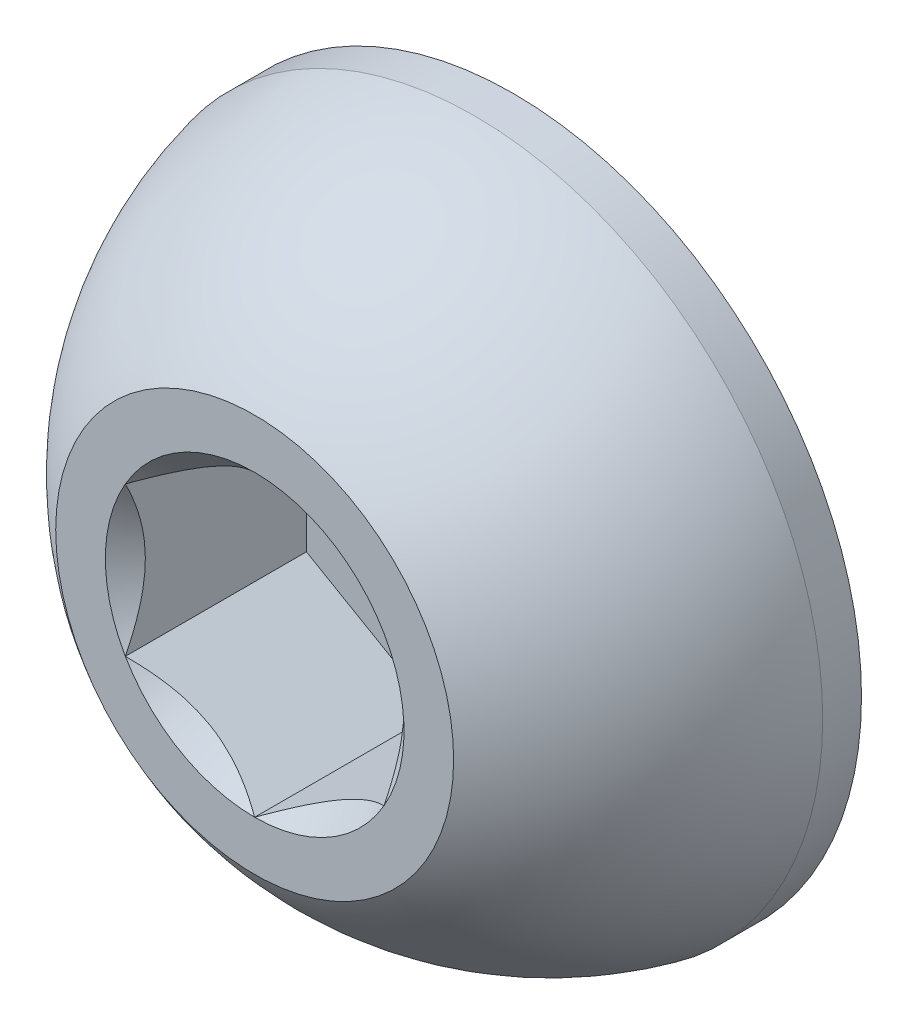
SolidWorks part; units mm, degrees
material "Stainless Steel (ferritic)"
ref_plane "Front" through (0, 0, 0) normal (0, 0, 1) x (1, 0, 0)
ref_plane "Top" through (0, 0, 0) normal (0, 1, 0) x (1, 0, 0)
ref_plane "Right" through (0, 0, 0) normal (1, 0, 0) x (0, 0, -1)
sketch "Sketch1" plane through (0, 0, 0) normal (1, 0, 0) x (0, 0, -1)
  line L2 (1.3, 1) -> (5.3, 1)
  line L3 (5.3, 1) -> (5.3, 0)
  line L4 (5.3, 0) -> (1.3, 0)
  line L6 (1.105, 1.75) -> (1.3, 1.75) construction
  line L7 (5.3, 1) -> (5.3, -1) construction
  line L8 (0, 0) -> (1.3, 0) construction
  line L9 (1.3, 1.75) -> (1.3, -1.75) construction
  line L11 (1.3, 1) -> (1.3, 0)
  line L13 (0, 0.65) -> (0, -0.65) construction
  line L14 (0, 0.65) -> (0, 1) construction
  line L15 (5.275, 1.0433) -> (5.475, 0.6969) construction
  line L16 (5.475, 0.6969) -> (5.675, 1.0433) construction
  line L17 (5.675, 1.0433) -> (5.275, 1.0433) construction
  line L18 (5.3, 1) -> (5.65, 1) construction
  line L19 (5.475, 1.0433) -> (5.475, 1) construction
  line L20 (5.475, 1) -> (5.475, 0.7402) construction
  line L21 (5.475, 0.7402) -> (5.475, 0.6969) construction
  line L22 (5.45, 0.7402) -> (5.5, 0.7402)
  line L23 (5.2875, 1.0217) -> (5.6625, 1.0217)
  line L24 (5.5, 0.7402) -> (5.6625, 1.0217)
  line L25 (5.45, 0.7402) -> (5.2875, 1.0217)
  line L26 (5, 1) -> (5.3, 0.7)
  arc A3 (0, 1) -> (1.105, 1.75) centre (1.4858, 0) cw construction
  point P29 (5.475, 1.0217)
  point P30 (4.3, -1)
  dimension "D1" = 0.195
  dimension "Pitch" = 0.4
  dimension "D3" = 0.05
  dimension "D2" = 0.3
  dimension "D4" = 45
  dimension "D5" = 1
sketch "Sketch7" plane through (0, 0, 0) normal (1, 0, 0) x (0, 0, -1)
  line L6 (1.105, 1.75) -> (1.3, 1.75) construction
  line L8 (0, 0) -> (1.3, 0) construction
  line L11 (1.3, 1.75) -> (1.3, -1.75) construction
  line L12 (1.105, 1.75) -> (1.3, 1.75)
  line L13 (0, 0) -> (1.3, 0)
  line L14 (0, 0.65) -> (0, -0.65) construction
  line L15 (1.3, 1.75) -> (1.3, 0)
  line L16 (0, 1) -> (0, 0)
  arc A2 (1.105, 1.75) -> (0, 1) centre (1.4858, 0) ccw construction
  arc A3 (1.105, 1.75) -> (0, 1) centre (1.4858, 0) ccw
revolve "Revolve2" add sketch "Sketch7" angle 360 mid plane about L13
sketch "Sketch5" plane through (0, 0, 0) normal (0, 0, 1) x (1, 0, 0)
  line L1 (0.65, -0.3753) -> (0.65, 0.3753)
  line L2 (0.65, 0.3753) -> (0, 0.7506)
  line L3 (0, 0.7506) -> (-0.65, 0.3753)
  line L4 (-0.65, 0.3753) -> (-0.65, -0.3753)
  line L5 (-0.65, -0.3753) -> (0, -0.7506)
  line L6 (0, -0.7506) -> (0.65, -0.3753)
  circle A0 centre (0, 0) radius 0.65 construction
extrude "Cut-Extrude2" cut sketch "Sketch5" against normal blind 0.91
sketch "Sketch6" plane through (0, 0, 0) normal (0, 0, 1) x (1, 0, 0)
  circle A0 centre (0, 0) radius 0.7506
extrude "Cut-Extrude3" cut sketch "Sketch6" against normal blind 0.91 draft 45
equation "\"D1@Cut-Extrude2\" = \"Head Ht@Sketch1\" * .7"
equation "\"D1@Sketch1\" = \"Head Ht@Sketch1\" * .15"
equation "\"D1@Cut-Extrude3\" = \"D1@Cut-Extrude2\""
equation "\"D3@Sketch1\" = \"Pitch@Sketch1\" / 8"
equation "\"D2@Sketch1\"=\"Pitch@Sketch1\"*0.75"
equation "\"D5@Sketch1\"=\"Pitch@Sketch1\"*2.5"
